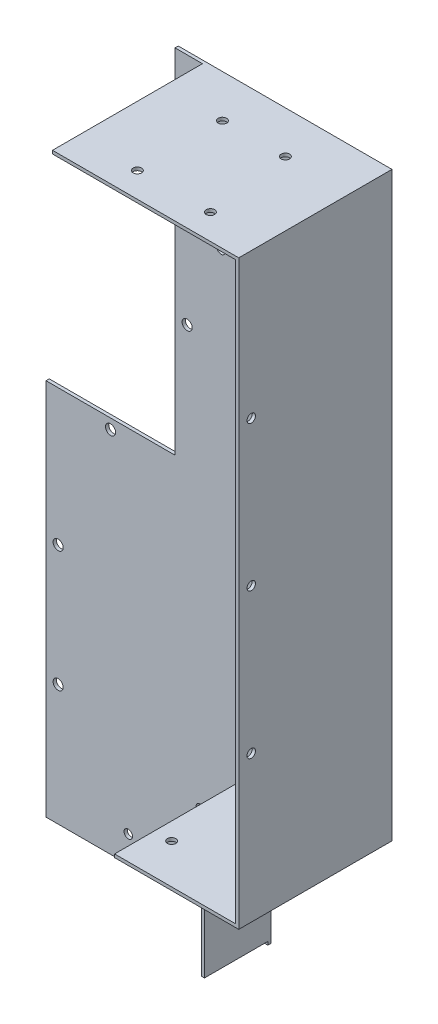
SolidWorks part; units mm, degrees
material "ABS PC"
ref_plane "Front Plane" through (0, 0, 0) normal (0, 0, 1) x (1, 0, 0)
ref_plane "Top Plane" through (0, 0, 0) normal (0, 1, 0) x (1, 0, 0)
ref_plane "Right Plane" through (0, 0, 0) normal (1, 0, 0) x (0, 0, -1)
sketch "Sketch1" plane through (0, 0, 0) normal (0, 0, 1) x (1, 0, 0)
  line L1 (0, 0) -> (170, 0)
  line L2 (0, 0) -> (0, 330)
  line L3 (0, 330) -> (170, 330)
  line L4 (170, 0) -> (170, 330)
  dimension "D1" = 170
  dimension "D2" = 330
extrude "Boss-Extrude1" add sketch "Sketch1" along normal blind 1.6
sketch "Sketch2" plane through (0, 0, 0) normal (0, 0, -1) x (-1, 0, 0)
  line L0 (0, 330) -> (-64, 330)
  line L2 (-170, 330) -> (0, 330) construction
  line L3 (-64, 330) -> (-64, 155)
  line L4 (-64, 155) -> (0, 155)
  line L5 (0, 330) -> (0, 0) construction
  line L6 (0, 330) -> (0, 155)
  dimension "D1" = 64
  dimension "D2" = 175
extrude "Cut-Extrude1" cut sketch "Sketch2" against normal blind 10
sketch "Sketch3" plane through (0, 0, 1.6) normal (0, 0, 1) x (1, 0, 0)
  line L0 (170, 330) -> (77.6, 330)
  line L1 (170, 330) -> (64, 330) construction
  line L2 (77.6, 330) -> (77.6, 328.4)
  line L3 (77.6, 328.4) -> (168.4, 328.4)
  line L4 (170, 0) -> (139.8364, 0)
  line L5 (0, 0) -> (170, 0) construction
  line L6 (170, 330) -> (170, 1.6)
  line L7 (170, 0) -> (170, 330) construction
  line L8 (168.4, 1.6) -> (168.4, 328.4)
  line L9 (168.4, 1.6) -> (170, 1.6)
  line M12 (170, 0) -> (170, 330)
  line M13 (170, 330) -> (64, 330)
  dimension "D3" = 1.6
  dimension "D1" = 92.4
  dimension "D2" = 1.6
  dimension "D4" = 1.6
extrude "Boss-Extrude2" add sketch "Sketch3" along normal blind 74.4 contours L8 L9 L2 L3 M12 M13
sketch "Sketch5" plane through (0, 0, 0) normal (0, -1, 0) x (1, 0, 0)
  line L0 (0, 0) -> (0, 1.6)
  line L1 (0, 1.6) -> (168.4, 1.6) construction
  line L2 (0, 1.6) -> (170, 1.6)
  line L3 (170, 76) -> (170, 0) construction
  line L4 (170, 1.6) -> (170, 0)
  line L5 (170, 0) -> (0, 0)
extrude "Boss-Extrude5" add sketch "Sketch5" along normal blind 32.5
sketch "Sketch6" plane through (0, 0, 0) normal (0, -1, 0) x (1, 0, 0)
  line L0 (168.4, 76) -> (170, 76)
  line L1 (170, 76) -> (170, 1.6)
  line L2 (170, 1.6) -> (168.4, 1.6)
  line L3 (168.4, 1.6) -> (168.4, 76)
extrude "Boss-Extrude6" add sketch "Sketch6" along normal blind 30.9
sketch "Sketch7" plane through (170, 0, 0) normal (1, 0, 0) x (0, 0, -1)
  line L0 (-76, -30.9) -> (-76, 41.5)
  line L1 (-76, -30.9) -> (-76, 330) construction
  line L2 (-76, 41.5) -> (-35, 41.5)
  line L3 (-35, 41.5) -> (-35, -30.9)
  line L4 (-1.6, -30.9) -> (-76, -30.9) construction
  line L5 (-35, -30.9) -> (-76, -30.9)
  dimension "D1" = 72.4
  dimension "D2" = 41
extrude "Cut-Extrude2" cut sketch "Sketch7" against normal blind 94
sketch "Sketch10" plane through (0, 0, 35) normal (0, 0, 1) x (1, 0, 0)
  line L0 (170, 41.5) -> (170, -32.5)
  line L1 (170, -32.5) -> (110, -32.5)
  line L2 (170, -32.5) -> (0, -32.5) construction
  line L3 (110, -32.5) -> (110, 41.5)
  line L4 (110, 41.5) -> (170, 41.5)
  dimension "D1" = 60
extrude "Cut-Extrude4" cut sketch "Sketch10" against normal up to surface (35 mm away)
sketch "Sketch13" plane through (0, 0, 1.6) normal (0, 0, 1) x (1, 0, 0)
  line L0 (110, -32.5) -> (55, -32.5)
  line L1 (110, -32.5) -> (0, -32.5) construction
  line L2 (110, 41.5) -> (110, -30.9)
  line L3 (110, -32.5) -> (110, 41.5) construction
  line L4 (110, 41.5) -> (108.4, 41.5)
  line L5 (108.4, 41.5) -> (108.4, -30.9)
  line L6 (108.4, -30.9) -> (110, -30.9)
  dimension "D2" = 1.6
  dimension "D1" = 1.6
extrude "Boss-Extrude9" add sketch "Sketch13" along normal blind 31.4 contours L2 L6 L5 L4
sketch "Sketch14" plane through (0, 0, 1.6) normal (0, 0, 1) x (1, 0, 0)
  line L0 (168.4, 41.5) -> (108.4, 41.5)
  line L1 (108.4, 41.5) -> (108.4, 43.1)
  line L2 (108.4, 43.1) -> (168.4, 43.1)
  line L3 (168.4, 41.5) -> (168.4, 328.4) construction
  line L4 (168.4, 43.1) -> (168.4, 41.5)
  dimension "D1" = 1.6
extrude "Boss-Extrude10" add sketch "Sketch14" along normal up to surface (74.4 mm away)
sketch "Sketch15" plane through (0, 330, 0) normal (0, 1, 0) x (1, 0, 0)
  circle A0 centre (107.0426, -21.1227) radius 2.1
  circle A1 centre (107.3201, -63.6218) radius 2.1
  circle A2 centre (143.3193, -63.3868) radius 2.1
  circle A3 centre (138.042, -20.9203) radius 2.1
extrude "Cut-Extrude5" cut sketch "Sketch15" against normal blind 2
sketch "Sketch16" plane through (0, 0, 1.6) normal (0, 0, 1) x (1, 0, 0)
  circle A0 centre (86.8435, 254.836) radius 2.1
  circle A1 centre (158.8435, 254.836) radius 2.1
extrude "Cut-Extrude6" cut sketch "Sketch16" against normal blind 2
sketch "Sketch17" plane through (0, 0, 1.6) normal (0, 0, 1) x (1, 0, 0)
  circle A0 centre (125.9178, 122.3874) radius 2.1
  circle A1 centre (103.9178, 122.3874) radius 2.1
  circle A2 centre (139.9481, 141.4705) radius 1.75
  circle A3 centre (139.9481, 158.4705) radius 1.75
  circle A4 centre (95.9481, 141.4705) radius 1.75
  circle A5 centre (95.9481, 158.4705) radius 1.75
extrude "Cut-Extrude7" cut sketch "Sketch17" against normal blind 6
sketch "Sketch18" plane through (0, 0, 1.6) normal (0, 0, 1) x (1, 0, 0)
  circle A0 centre (130.2837, 71.4604) radius 2.1
extrude "Cut-Extrude8" cut sketch "Sketch18" against normal blind 6
sketch "Sketch20" plane through (0, 0, 1.6) normal (0, 0, 1) x (1, 0, 0)
  circle A0 centre (40.7837, -19.3396) radius 2.1
extrude "Cut-Extrude10" cut sketch "Sketch20" against normal blind 40
sketch "Sketch21" plane through (0, 0, 1.6) normal (0, 0, 1) x (1, 0, 0)
  circle A0 centre (6, 27.5) radius 2.5
  circle A1 centre (6, 87.5) radius 2.5
  circle A2 centre (32, 150) radius 2.5
  circle A3 centre (70, 214) radius 2.5
  circle A4 centre (70, 272) radius 2.5
extrude "Cut-Extrude11" cut sketch "Sketch21" against normal blind 10
sketch "Sketch22" plane through (170, 0, 0) normal (1, 0, 0) x (0, 0, -1)
  circle A0 centre (-69.8, 114) radius 2.1
  circle A1 centre (-69.8, 186) radius 2.1
  circle A2 centre (-69.8, 258) radius 2.1
extrude "Cut-Extrude12" cut sketch "Sketch22" against normal blind 4
sketch "Sketch23" plane through (0, 41.5, 0) normal (0, -1, 0) x (1, 0, 0)
  circle A0 centre (117, 56.3) radius 2.1
extrude "Cut-Extrude13" cut sketch "Sketch23" against normal blind 4
sketch "Sketch24" plane through (0, 0, 1.6) normal (0, 0, 1) x (1, 0, 0)
  circle A0 centre (96.0127, 83.0819) radius 1.75
  circle A1 centre (96.0127, 95.0819) radius 2.1
extrude "Cut-Extrude14" cut sketch "Sketch24" against normal blind 10
sketch "Sketch25" plane through (0, 0, 1.6) normal (0, 0, 1) x (1, 0, 0)
  circle A0 centre (88.2189, 9.5819) radius 2.1
  circle A1 centre (76.2189, 9.5819) radius 1.75
extrude "Cut-Extrude15" cut sketch "Sketch25" against normal blind 10
